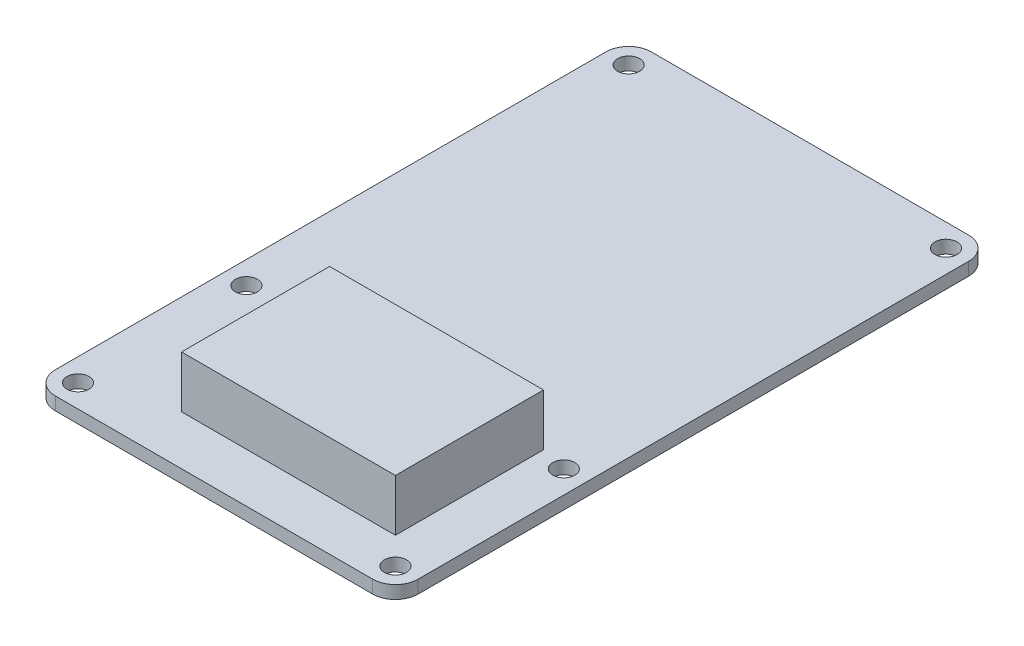
SolidWorks part; units mm, degrees
ref_plane "Front Plane" through (0, 0, 0) normal (0, 0, 1) x (1, 0, 0)
ref_plane "Top Plane" through (0, 0, 0) normal (0, 1, 0) x (1, 0, 0)
ref_plane "Right Plane" through (0, 0, 0) normal (1, 0, 0) x (0, 0, -1)
sketch "Sketch1" plane through (0, 0, 0) normal (0, 1, 0) x (1, 0, 0)
  line L1 (24.5, 46) -> (-24.5, 46)
  line L2 (28, 42.5) -> (28, -42.5)
  line L3 (24.5, -46) -> (-24.5, -46)
  line L4 (-28, 42.5) -> (-28, -42.5)
  line L5 (28, 46) -> (-28, -46) construction
  line L6 (28, -46) -> (-28, 46) construction
  arc A0 (28, -42.5) -> (24.5, -46) centre (24.5, -42.5) cw
  arc A1 (-24.5, -46) -> (-28, -42.5) centre (-24.5, -42.5) cw
  arc A2 (24.5, 46) -> (28, 42.5) centre (24.5, 42.5) cw
  arc A3 (-24.5, 46) -> (-28, 42.5) centre (-24.5, 42.5) ccw
  point P0 (0, 0)
  dimension "D3" = 3.5
  dimension "D1" = 56
  dimension "D2" = 92
extrude "Boss-Extrude1" add sketch "Sketch1" along normal blind 2
sketch "Sketch2" plane through (0, 0, 0) normal (0, -1, 0) x (1, 0, 0)
  line L1 (-12.64, 15.52) -> (20.38, 15.52)
  line L2 (-12.64, 15.52) -> (-12.64, 38.38)
  line L3 (-12.64, 38.38) -> (20.38, 38.38)
  line L4 (20.38, 15.52) -> (20.38, 38.38)
  line L5 (-12.64, 15.52) -> (20.38, 38.38) construction
  line L6 (-12.64, 38.38) -> (20.38, 15.52) construction
  line L8 (-24.5, 46) -> (24.5, 46) construction
  line L9 (28, 42.5) -> (28, -42.5) construction
  point P0 (3.87, 26.95)
  point P11 (-25.6069, 68.1307)
  dimension "D1" = 7.62
  dimension "D2" = 33.02
  dimension "D3" = 22.86
  dimension "D4" = 7.62
extrude "Boss-Extrude2" add sketch "Sketch2" against normal blind 10 contours L3 L4 L1 L2
hole_wizard "M3 Clearance Hole1" positions "Sketch3" profile "Sketch4" hole size "M3" standard "ANSI Metric" end condition through all
sketch "Sketch3" plane through (0, 0, 0) normal (0, -1, 0) x (-1, 0, 0)
  arc A0 (28, 42.5) -> (24.5, 46) centre (24.5, 42.5) ccw construction
  arc A1 (-24.5, 46) -> (-28, 42.5) centre (-24.5, 42.5) ccw construction
  arc A2 (-28, -42.5) -> (-24.5, -46) centre (-24.5, -42.5) ccw construction
  arc A3 (24.5, -46) -> (28, -42.5) centre (24.5, -42.5) ccw construction
  point P0 (-24.5, -42.5)
  point P2 (24.5, -42.5)
  point P4 (24.5, -16.5)
  point P6 (-24.5, -16.5)
  point P8 (-24.5, 42.5)
  point P10 (24.5, 42.5)
  point P13 (0, 0)
  point P18 (0, 0)
  point P22 (0, 0)
  point P26 (0, 0)
  point P30 (0, 0)
  point P31 (0, 0)
  point P32 (0, 0)
  point P33 (0, 0)
  point P34 (0, 0)
  dimension "D1" = 26
sketch "Sketch4" plane through (24.5, 0, 42.5) normal (1, 0, 0) x (0, 0, -1)
  line L0 (0, 0) -> (0, 10)
  line L1 (0, 10) -> (1.7, 10)
  line L2 (1.7, 10) -> (1.7, 0)
  line L5 (1.7, 0) -> (0, 0)
  line L11 (0, -6.35) -> (0, 107.95) construction
  dimension "Thru Hole Dia." = 3.4
  dimension "Thru Hole Depth" = 10
